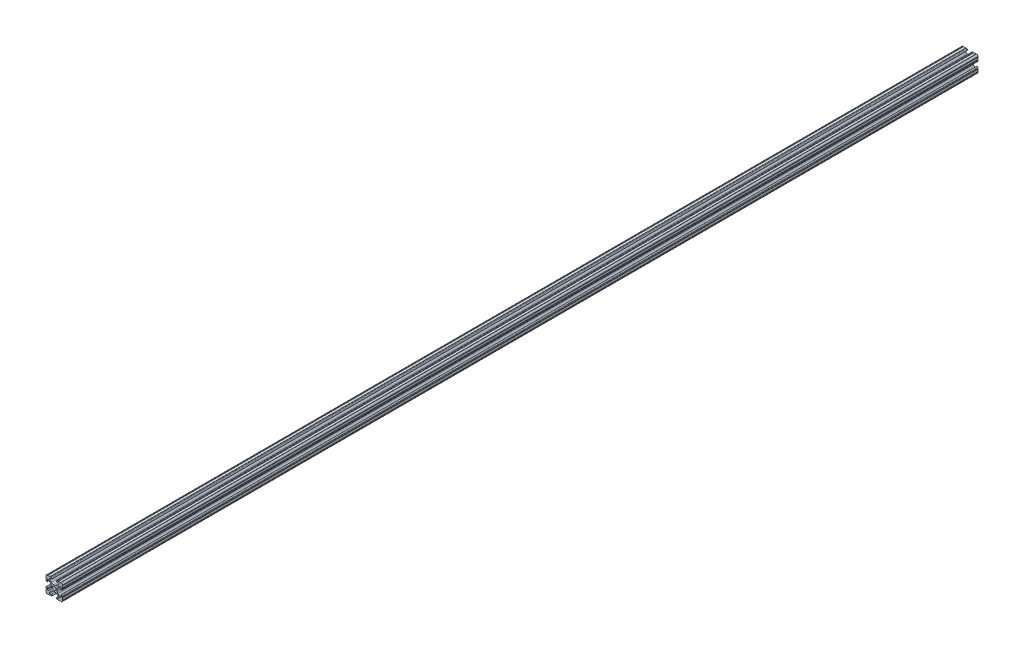
SolidWorks part; units mm, degrees
ref_plane "Front Plane" through (0, 0, 0) normal (0, 0, 1) x (1, 0, 0)
ref_plane "Top Plane" through (0, 0, 0) normal (0, 1, 0) x (1, 0, 0)
ref_plane "Right Plane" through (0, 0, 0) normal (1, 0, 0) x (0, 0, -1)
sketch "Sketch1" plane through (0, 0, 0) normal (0, 0, 1) x (1, 0, 0)
  line L0 (0, 12.7) -> (-12.7814, 12.7) construction
  line L1 (-4.5085, 0) -> (-4.5085, 2.9459)
  line L2 (-6.0437, 12.5461) -> (-10.0976, 12.6876) construction
  line L3 (-11.5616, 12.4229) -> (-4.3159, 12.1699) construction
  line L4 (-6.4364, 10.3486) -> (-6.3592, 12.5571) construction
  line L6 (-2.9459, 4.5085) -> (0, 4.5085)
  line L7 (0, 0) -> (0, 12.7) construction
  line L8 (0, 0) -> (-12.7814, 0) construction
  line L9 (0.7813, 0.7813) -> (-0.7813, -0.7813) construction
  line L10 (-2.9459, 4.5085) -> (-7.1484, 8.711)
  line L11 (-4.5085, 2.9459) -> (-8.711, 7.1484)
  line L13 (0, 0) -> (-12.7814, 12.7814) construction
  line L14 (-10.4131, 12.6987) -> (-4.3048, 12.4853)
  line L15 (-4.3048, 12.4853) -> (-4.382, 10.2769) construction
  line L16 (-4.382, 10.2769) -> (-6.4364, 10.3486)
  line L17 (-12.6987, 10.4131) -> (-12.4853, 4.3048)
  line L18 (-10.2769, 4.382) -> (-10.3486, 6.4364)
  circle A0 centre (0, 0) radius 2.6035
  arc A1 (-4.382, 10.2769) -> (-4.3048, 12.4853) centre (-4.3434, 11.3811) ccw
  arc A2 (-7.1484, 8.711) -> (-6.4364, 10.3486) centre (-6.4698, 9.3896) cw
  arc A3 (-8.711, 7.1484) -> (-10.3486, 6.4364) centre (-9.3896, 6.4698) ccw
  arc A4 (-10.2769, 4.382) -> (-12.4853, 4.3048) centre (-11.3811, 4.3434) cw
  arc A5 (-10.4131, 12.6987) -> (-12.6987, 10.4131) centre (-10.4902, 10.4902) ccw
  arc A6 (-10.4131, 12.6987) -> (-9.7821, 12.6766) centre (-10.0976, 12.6876) ccw
  arc A7 (-6.3592, 12.5571) -> (-5.7282, 12.5351) centre (-6.0437, 12.5461) ccw
  arc A8 (-12.5571, 6.3592) -> (-12.5351, 5.7282) centre (-12.5461, 6.0437) cw
  arc A9 (-12.6987, 10.4131) -> (-12.6766, 9.7821) centre (-12.6876, 10.0976) cw
  dimension "D1" = 5.207
  dimension "D5" = 14.859
  dimension "D9" = 2
  dimension "D2" = 25.4
  dimension "D12" = 0.6314
  dimension "D10" = 2.2098
  dimension "D3" = 9.017
  dimension "D4" = 9.017
  dimension "D6" = 25.4
  dimension "D7" = 6.477
  dimension "D8" = 2.2098
  dimension "D11" = 12.7
sketch "Sketch3" plane through (0, 0, 0) normal (0, 0, 1) x (1, 0, 0)
  line L0 (-2.9459, 4.5085) -> (0, 4.5085) construction
  line L1 (-2.9459, 4.5085) -> (-7.1484, 8.711) construction
  line L2 (-4.382, 10.2769) -> (-6.4364, 10.3486) construction
  line L3 (-10.4131, 12.6987) -> (-4.3048, 12.4853) construction
  line L4 (-4.5085, 0) -> (-4.5085, 2.9459) construction
  line L5 (-4.5085, 2.9459) -> (-8.711, 7.1484) construction
  line L6 (-10.2769, 4.382) -> (-10.3486, 6.4364) construction
  line L7 (-12.6987, 10.4131) -> (-12.4853, 4.3048) construction
  line L8 (-1.1153, 4.5085) -> (1.1153, 4.5085)
  line L9 (-4.2404, 5.803) -> (-7.1484, 8.711)
  line L10 (-4.382, 10.2769) -> (-6.4364, 10.3486)
  line L11 (-9.7821, 12.6766) -> (-6.3592, 12.5571)
  line L12 (-4.5085, -1.1153) -> (-4.5085, 1.1153)
  line L13 (-5.803, 4.2404) -> (-8.711, 7.1484)
  line L14 (-10.2769, 4.382) -> (-10.3486, 6.4364)
  line L15 (-12.6766, 9.7821) -> (-12.5571, 6.3592)
  line L16 (-5.7282, 12.5351) -> (-4.3048, 12.4853)
  line L17 (-12.5351, 5.7282) -> (-12.4853, 4.3048)
  line L18 (0, 0) -> (0, 12.7) construction
  line L19 (0, 0) -> (-12.7814, 0) construction
  line L20 (12.5351, 5.7282) -> (12.4853, 4.3048)
  line L21 (5.7282, 12.5351) -> (4.3048, 12.4853)
  line L22 (12.6766, 9.7821) -> (12.5571, 6.3592)
  line L23 (10.2769, 4.382) -> (10.3486, 6.4364)
  line L24 (5.803, 4.2404) -> (8.711, 7.1484)
  line L25 (4.5085, -1.1153) -> (4.5085, 1.1153)
  line L26 (9.7821, 12.6766) -> (6.3592, 12.5571)
  line L27 (4.382, 10.2769) -> (6.4364, 10.3486)
  line L28 (4.2404, 5.803) -> (7.1484, 8.711)
  line L29 (4.2404, -5.803) -> (7.1484, -8.711)
  line L30 (4.382, -10.2769) -> (6.4364, -10.3486)
  line L31 (9.7821, -12.6766) -> (6.3592, -12.5571)
  line L32 (5.803, -4.2404) -> (8.711, -7.1484)
  line L33 (10.2769, -4.382) -> (10.3486, -6.4364)
  line L34 (12.6766, -9.7821) -> (12.5571, -6.3592)
  line L35 (5.7282, -12.5351) -> (4.3048, -12.4853)
  line L36 (12.5351, -5.7282) -> (12.4853, -4.3048)
  line L37 (-12.5351, -5.7282) -> (-12.4853, -4.3048)
  line L38 (-5.7282, -12.5351) -> (-4.3048, -12.4853)
  line L39 (-12.6766, -9.7821) -> (-12.5571, -6.3592)
  line L40 (-10.2769, -4.382) -> (-10.3486, -6.4364)
  line L41 (-5.803, -4.2404) -> (-8.711, -7.1484)
  line L42 (-9.7821, -12.6766) -> (-6.3592, -12.5571)
  line L43 (-4.382, -10.2769) -> (-6.4364, -10.3486)
  line L44 (-4.2404, -5.803) -> (-7.1484, -8.711)
  line L45 (-1.1153, -4.5085) -> (1.1153, -4.5085)
  arc A0 (-10.4131, 12.6987) -> (-9.7821, 12.6766) centre (-10.0976, 12.6876) ccw construction
  arc A1 (-6.4364, 10.3486) -> (-7.1484, 8.711) centre (-6.4698, 9.3896) ccw construction
  arc A2 (-4.382, 10.2769) -> (-4.3048, 12.4853) centre (-4.3434, 11.3811) ccw construction
  arc A3 (-8.711, 7.1484) -> (-10.3486, 6.4364) centre (-9.3896, 6.4698) ccw construction
  arc A4 (-12.4853, 4.3048) -> (-10.2769, 4.382) centre (-11.3811, 4.3434) ccw construction
  arc A5 (-6.3592, 12.5571) -> (-5.7282, 12.5351) centre (-6.0437, 12.5461) ccw construction
  arc A6 (-10.4131, 12.6987) -> (-12.6987, 10.4131) centre (-10.4902, 10.4902) ccw construction
  arc A7 (-12.6766, 9.7821) -> (-12.6987, 10.4131) centre (-12.6876, 10.0976) ccw construction
  arc A8 (-12.5351, 5.7282) -> (-12.5571, 6.3592) centre (-12.5461, 6.0437) ccw construction
  arc A9 (-10.4131, 12.6987) -> (-9.7821, 12.6766) centre (-10.0976, 12.6876) ccw
  arc A10 (-6.4364, 10.3486) -> (-7.1484, 8.711) centre (-6.4698, 9.3896) ccw
  arc A11 (-4.382, 10.2769) -> (-4.3048, 12.4853) centre (-4.3434, 11.3811) ccw
  arc A12 (-8.711, 7.1484) -> (-10.3486, 6.4364) centre (-9.3896, 6.4698) ccw
  arc A13 (-12.4853, 4.3048) -> (-10.2769, 4.382) centre (-11.3811, 4.3434) ccw
  arc A14 (-6.3592, 12.5571) -> (-5.7282, 12.5351) centre (-6.0437, 12.5461) ccw
  arc A15 (-10.4131, 12.6987) -> (-12.6987, 10.4131) centre (-10.4902, 10.4902) ccw
  arc A16 (-12.6766, 9.7821) -> (-12.6987, 10.4131) centre (-12.6876, 10.0976) ccw
  arc A17 (-12.5351, 5.7282) -> (-12.5571, 6.3592) centre (-12.5461, 6.0437) ccw
  arc A18 (-1.1153, 4.5085) -> (-4.2404, 5.803) centre (-1.1153, 8.9281) cw
  arc A19 (4.5085, 1.1153) -> (5.803, 4.2404) centre (8.9281, 1.1153) cw
  arc A20 (1.1153, 4.5085) -> (4.2404, 5.803) centre (1.1153, 8.9281) ccw
  arc A21 (-4.5085, 1.1153) -> (-5.803, 4.2404) centre (-8.9281, 1.1153) ccw
  arc A22 (12.5351, 5.7282) -> (12.5571, 6.3592) centre (12.5461, 6.0437) cw
  arc A23 (12.6766, 9.7821) -> (12.6987, 10.4131) centre (12.6876, 10.0976) cw
  arc A24 (10.4131, 12.6987) -> (12.6987, 10.4131) centre (10.4902, 10.4902) cw
  arc A25 (6.3592, 12.5571) -> (5.7282, 12.5351) centre (6.0437, 12.5461) cw
  arc A26 (12.4853, 4.3048) -> (10.2769, 4.382) centre (11.3811, 4.3434) cw
  arc A27 (8.711, 7.1484) -> (10.3486, 6.4364) centre (9.3896, 6.4698) cw
  arc A28 (4.382, 10.2769) -> (4.3048, 12.4853) centre (4.3434, 11.3811) cw
  arc A29 (6.4364, 10.3486) -> (7.1484, 8.711) centre (6.4698, 9.3896) cw
  arc A30 (10.4131, 12.6987) -> (9.7821, 12.6766) centre (10.0976, 12.6876) cw
  arc A31 (10.4131, -12.6987) -> (9.7821, -12.6766) centre (10.0976, -12.6876) ccw
  arc A32 (6.4364, -10.3486) -> (7.1484, -8.711) centre (6.4698, -9.3896) ccw
  arc A33 (4.382, -10.2769) -> (4.3048, -12.4853) centre (4.3434, -11.3811) ccw
  arc A34 (8.711, -7.1484) -> (10.3486, -6.4364) centre (9.3896, -6.4698) ccw
  arc A35 (12.4853, -4.3048) -> (10.2769, -4.382) centre (11.3811, -4.3434) ccw
  arc A36 (6.3592, -12.5571) -> (5.7282, -12.5351) centre (6.0437, -12.5461) ccw
  arc A37 (10.4131, -12.6987) -> (12.6987, -10.4131) centre (10.4902, -10.4902) ccw
  arc A38 (12.6766, -9.7821) -> (12.6987, -10.4131) centre (12.6876, -10.0976) ccw
  arc A39 (12.5351, -5.7282) -> (12.5571, -6.3592) centre (12.5461, -6.0437) ccw
  arc A40 (-4.5085, -1.1153) -> (-5.803, -4.2404) centre (-8.9281, -1.1153) cw
  arc A41 (1.1153, -4.5085) -> (4.2404, -5.803) centre (1.1153, -8.9281) cw
  arc A42 (4.5085, -1.1153) -> (5.803, -4.2404) centre (8.9281, -1.1153) ccw
  arc A43 (-1.1153, -4.5085) -> (-4.2404, -5.803) centre (-1.1153, -8.9281) ccw
  arc A44 (-12.5351, -5.7282) -> (-12.5571, -6.3592) centre (-12.5461, -6.0437) cw
  arc A45 (-12.6766, -9.7821) -> (-12.6987, -10.4131) centre (-12.6876, -10.0976) cw
  arc A46 (-10.4131, -12.6987) -> (-12.6987, -10.4131) centre (-10.4902, -10.4902) cw
  arc A47 (-6.3592, -12.5571) -> (-5.7282, -12.5351) centre (-6.0437, -12.5461) cw
  arc A48 (-12.4853, -4.3048) -> (-10.2769, -4.382) centre (-11.3811, -4.3434) cw
  arc A49 (-8.711, -7.1484) -> (-10.3486, -6.4364) centre (-9.3896, -6.4698) cw
  arc A50 (-4.382, -10.2769) -> (-4.3048, -12.4853) centre (-4.3434, -11.3811) cw
  arc A51 (-6.4364, -10.3486) -> (-7.1484, -8.711) centre (-6.4698, -9.3896) cw
  arc A52 (-10.4131, -12.6987) -> (-9.7821, -12.6766) centre (-10.0976, -12.6876) cw
  circle A53 centre (0, 0) radius 2.6035 construction
  circle A54 centre (0, 0) radius 2.6035
  point P135 (4.5085, 0)
  dimension "D2" = 4.4196
extrude "Extrude1" add sketch "Sketch3" along normal mid plane 1422.4
equation "\"D10@Sketch1\" = \"D8@Sketch1\""
equation "\"D11@Sketch1\" = \"D6@Sketch1\"/2"
equation "\"D12@Sketch1\" = \"D8@Sketch1\"/3.5"
equation "\"D2@Sketch3\" = \"D8@Sketch1\"*2"
